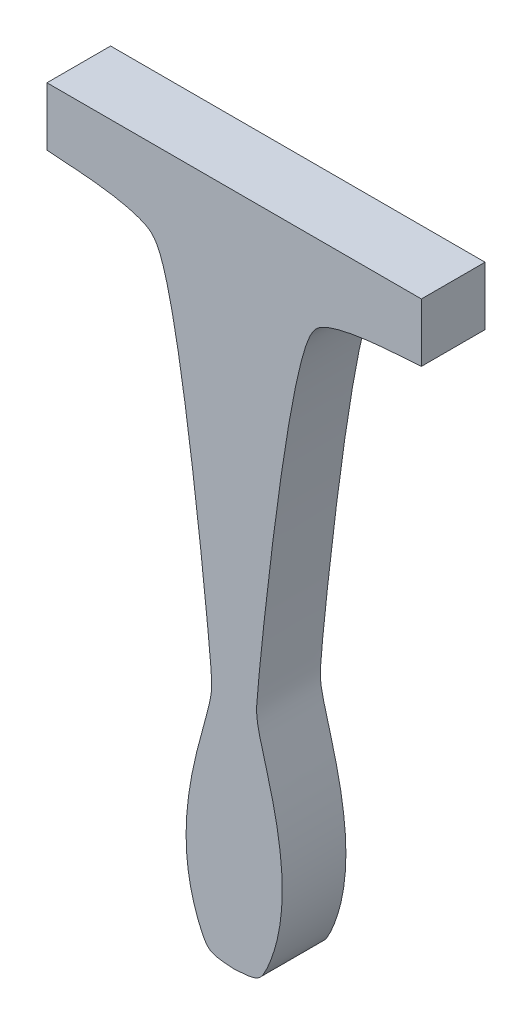
SolidWorks part; units mm, degrees
ref_plane "Plan de face" through (0, 0, 0) normal (0, 0, 1) x (1, 0, 0)
ref_plane "Plan de dessus" through (0, 0, 0) normal (0, 1, 0) x (1, 0, 0)
ref_plane "Plan de droite" through (0, 0, 0) normal (1, 0, 0) x (0, 0, -1)
sketch "Esquisse1" plane through (0, 0, 0) normal (0, 0, 1) x (1, 0, 0)
  line L0 (0, 0) -> (0, 1.7852) construction
  line L1 (0, 0) -> (0, 29.7342) construction
  line L2 (25, 24.6225) -> (-25, 24.6225)
  line L3 (-25, 24.6225) -> (-25, 16.8225)
  line L4 (25, 24.6225) -> (25, 16.8225)
  spline S0 degree 3 poles (-25, 16.8225) (-22.674, 16.5795) (-13.851, 16.4558) (-7.7, 11.8759) (-3.1307, -30.2471) (-2.7928, -37.2371) (-8.925, -51.7517) (-3.6998, -65.016) (-2.6988, -65.193) (0, -65.3775) knots 0 0 0 0 0.256783 0.320281 0.600019 0.665716 0.911555 0.948056 1 1 1 1
  spline S1 degree 3 poles (25, 16.8225) (22.674, 16.5795) (13.851, 16.4558) (7.7, 11.8759) (3.1307, -30.2471) (2.7928, -37.2371) (8.925, -51.7517) (3.6998, -65.016) (2.6988, -65.193) (0, -65.3775) knots 0 0 0 0 0.256783 0.320281 0.600019 0.665716 0.911555 0.948056 1 1 1 1
  point P17 (0, 24.6225)
  dimension "D1" = 25
  dimension "D2" = 7.8
  dimension "D3" = 4.25
  dimension "D4" = 3
  dimension "D5" = 2
  dimension "D6" = 90
extrude "Boss.-Extru.1" add sketch "Esquisse1" along normal blind 8.5
equation "\"8.5.00mm\"=10"
